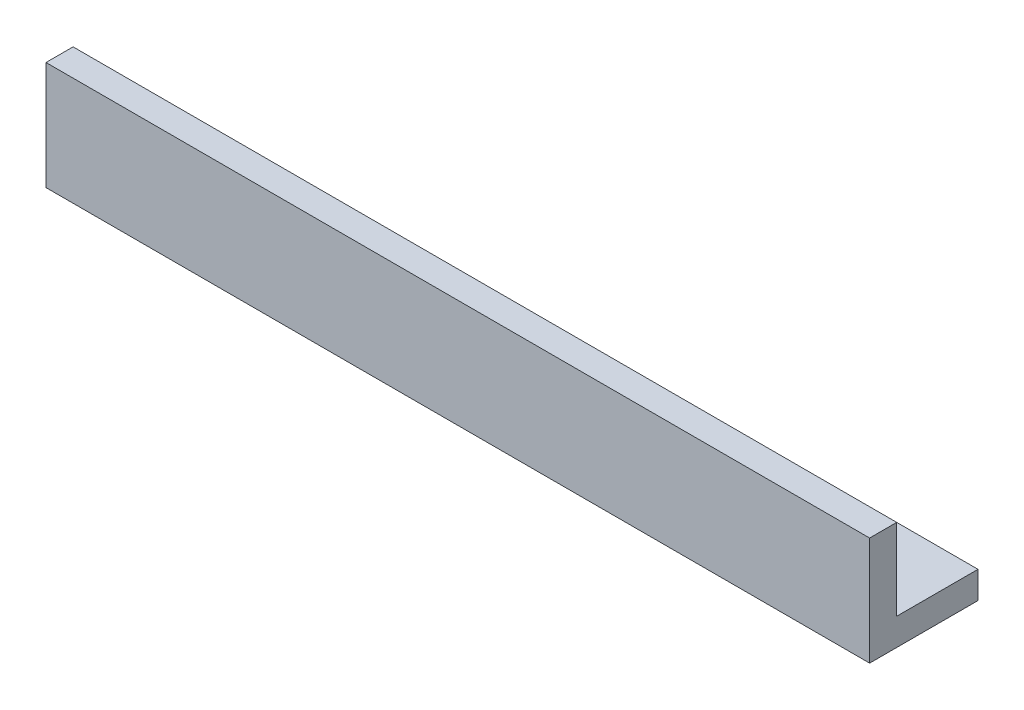
SolidWorks part; units mm, degrees
ref_plane "Front Plane" through (0, 0, 0) normal (0, 0, 1) x (1, 0, 0)
ref_plane "Top Plane" through (0, 0, 0) normal (0, 1, 0) x (1, 0, 0)
ref_plane "Right Plane" through (0, 0, 0) normal (1, 0, 0) x (0, 0, -1)
sketch "Sketch1" plane through (0, 0, 0) normal (0, 0, 1) x (1, 0, 0)
  line L1 (-24.7335, 28.7043) -> (71.7865, 28.7043)
  line L2 (-24.7335, 28.7043) -> (-24.7335, 16.0043)
  line L3 (-24.7335, 16.0043) -> (71.7865, 16.0043)
  line L4 (71.7865, 28.7043) -> (71.7865, 16.0043)
  dimension "D1" = 96.52
  dimension "D2" = 12.7
extrude "Boss-Extrude1" add sketch "Sketch1" along normal blind 3.175
ref_plane "Plane1" through (71.7865, 16.0043, 3.175) normal (1, 0, 0) x (0, 0, -1)
ref_plane "Plane2" through (-24.7335, 28.7043, 3.175) normal (0, 0, -1) x (-1, 0, 0)
ref_plane "Plane3" through (-24.7335, 16.0043, 3.175) normal (1, 0, 0) x (0, 0, -1)
sketch "Sketch7" plane through (0, 16.0043, 0) normal (0, -1, 0) x (-1, 0, 0)
  line L0 (24.7335, 0) -> (-71.7865, 0) construction
  line L1 (24.7335, 9.525) -> (-71.7865, 9.525)
  line L2 (24.7335, 9.525) -> (24.7335, 0)
  line L3 (24.7335, 0) -> (-71.7865, 0)
  line L4 (-71.7865, 9.525) -> (-71.7865, 0)
  dimension "D1" = 96.52
  dimension "D2" = 9.525
  dimension "D3" = 0
  dimension "D4" = 0
extrude "Boss-Extrude2" add sketch "Sketch7" against normal blind 3.175
